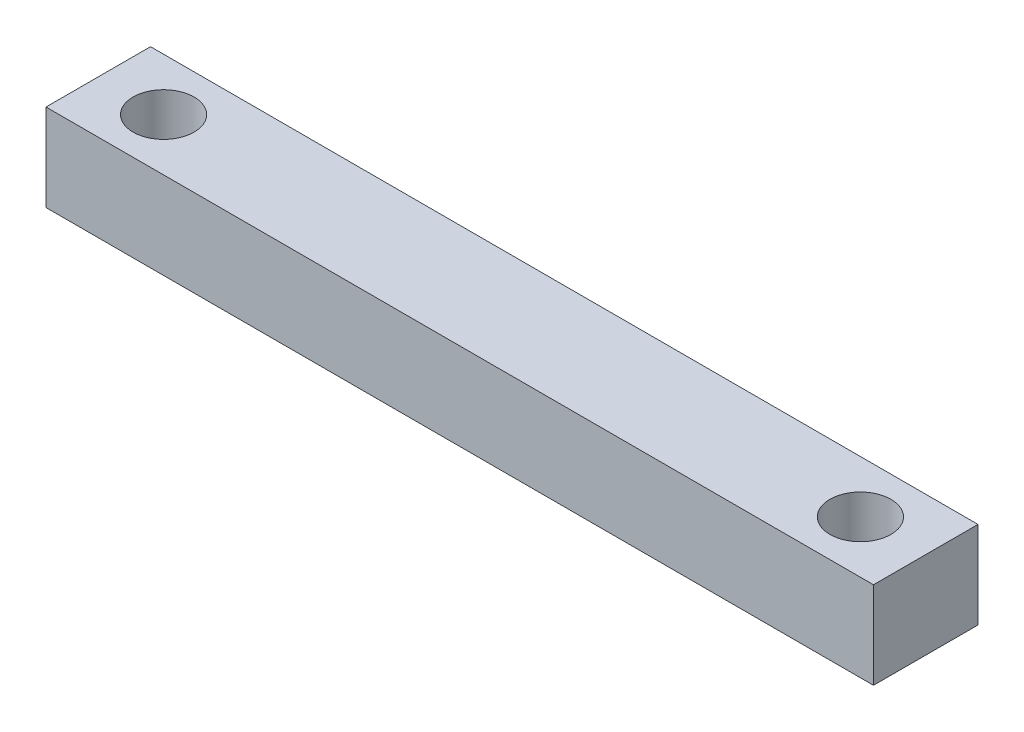
SolidWorks part; units mm, degrees
material "PLA"
ref_plane "Front Plane" through (0, 0, 0) normal (0, 0, 1) x (1, 0, 0)
ref_plane "Top Plane" through (0, 0, 0) normal (0, 1, 0) x (1, 0, 0)
ref_plane "Right Plane" through (0, 0, 0) normal (1, 0, 0) x (0, 0, -1)
sketch "Sketch1" plane through (0, 0, 0) normal (0, 1, 0) x (1, 0, 0)
  line L0 (-23.75, 0) -> (23.75, 0) construction
  line L1 (-23.75, -3) -> (23.75, -3)
  line L2 (-23.75, -3) -> (-23.75, 3)
  line L3 (-23.75, 3) -> (23.75, 3)
  line L4 (23.75, -3) -> (23.75, 3)
  line L5 (-23.75, -3) -> (23.75, 3) construction
  line L6 (-23.75, 3) -> (23.75, -3) construction
  circle A0 centre (-20, 0) radius 1.75
  circle A1 centre (20, 0) radius 1.75
  point P0 (0, 0)
  dimension "D1" = 3.5
  dimension "D2" = 40
  dimension "D3" = 20
  dimension "D5" = 3
  dimension "D4" = 3.75
extrude "Boss-Extrude1" add sketch "Sketch1" along normal blind 5
